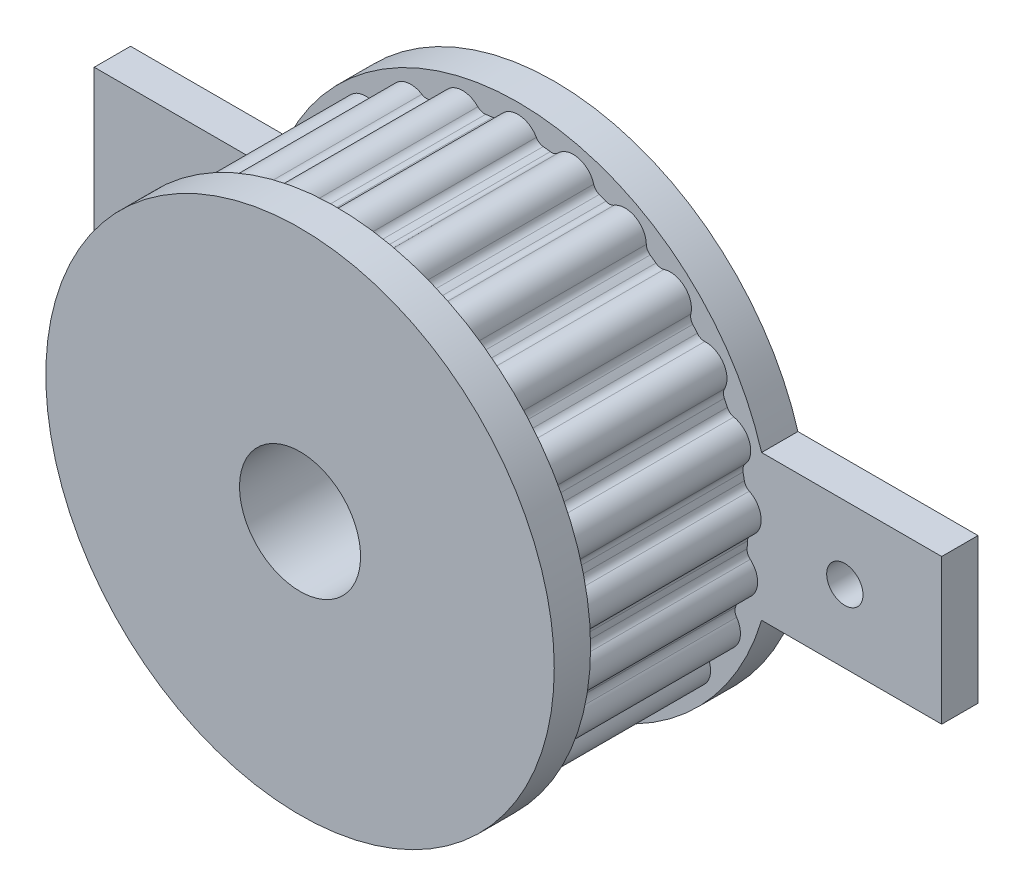
SolidWorks part; units mm, degrees
ref_plane "Plan de face" through (0, 0, 0) normal (0, 0, 1) x (1, 0, 0)
ref_plane "Plan de dessus" through (0, 0, 0) normal (0, 1, 0) x (1, 0, 0)
ref_plane "Plan de droite" through (0, 0, 0) normal (1, 0, 0) x (0, 0, -1)
sketch "Esquisse1" plane through (0, 0, 0) normal (0, 0, 1) x (1, 0, 0)
  circle A0 centre (0, 0) radius 21
  dimension "D1" = 42
extrude "Boss.-Extru.1" add sketch "Esquisse1" along normal blind 21
sketch "Esquisse2" plane through (0, 0, 0) normal (1, 0, 0) x (0, 0, -1)
  line L0 (0, 0) -> (-42, 0) construction
  line L1 (0, 0) -> (-21, 0)
  line L2 (-21, 0) -> (-21, 5)
  line L3 (-21, 21) -> (-21, -21) construction
  line L4 (-21, 5) -> (0, 5)
  line L5 (0, -21) -> (0, 21) construction
  line L6 (0, 5) -> (0, 0)
  dimension "D1" = 0
  dimension "D2" = 5
revolve "Enlèvement de matière-Révolution1" cut sketch "Esquisse2" angle 360 about L0
ref_plane "Plan1" through (0, 0, 18) normal (0, 0, 1) x (1, 0, 0)
sketch "Esquisse3" plane through (0, 0, 18) normal (0, 0, 1) x (1, 0, 0)
  circle A0 centre (0, 0) radius 18.985
  circle A1 centre (0, 0) radius 28.5
  dimension "D1" = 37.97
extrude "Enlèv. mat.-Extru.1" cut sketch "Esquisse3" against normal blind 15
sketch "Esquisse5" plane through (0, 0, 18) normal (0, 0, -1) x (-1, 0, 0)
  line L0 (0, 0) -> (0, 38.7923) construction
  line L1 (0, 38.7923) -> (-15.821, 18.985) construction
  line L2 (-15.821, 18.985) -> (15.2424, 18.985) construction
  line L3 (-3.2223, 20.125) -> (3.5661, 20.125) construction
  circle A0 centre (0, 0) radius 18.985 construction
  arc A1 (-1.6667, 18.9117) -> (1.6667, 18.9117) centre (0, 0) cw
  arc A2 (-1.6667, 18.9117) -> (1.6667, 18.9117) centre (0, 18.3736) cw
  dimension "D1" = 1.14
  dimension "D2" = 1.6667
extrude "Boss.-Extru.2" add sketch "Esquisse5" along normal up to surface (15 mm away) up to face at (18.985, 0, 3)
fillet "Congé1" radius 0.75 2 edges at (1.6667, 18.9117, 10.5) (-1.6667, 18.9117, 10.5)
pattern_circular "Répétition circulaire1" count 25 over 360 about axis through (0, 0, 0) along (0, 0, 1) of "Congé1", "Boss.-Extru.2"
sketch "Sketch2" plane through (0, 0, 0) normal (0, 0, -1) x (-1, 0, 0)
  line L0 (-35, -6) -> (35, -6)
  line L1 (-35, -6) -> (-35, 6)
  line L2 (-35, 6) -> (35, 6)
  line L3 (35, -6) -> (35, 6)
  line L4 (-35, -6) -> (35, 6) construction
  line L5 (-35, 6) -> (35, -6) construction
  circle A0 centre (-27, 0) radius 1.5
  circle A1 centre (27, 0) radius 1.5
  circle A2 centre (0, 0) radius 5
  point P0 (0, 0)
  dimension "D3" = 3
  dimension "D4" = 3
  dimension "D7" = 10
  dimension "D1" = 70
  dimension "D2" = 12
  dimension "D5" = 8
  dimension "D6" = 8
extrude "Boss-Extrude1" add sketch "Sketch2" against normal blind 3
